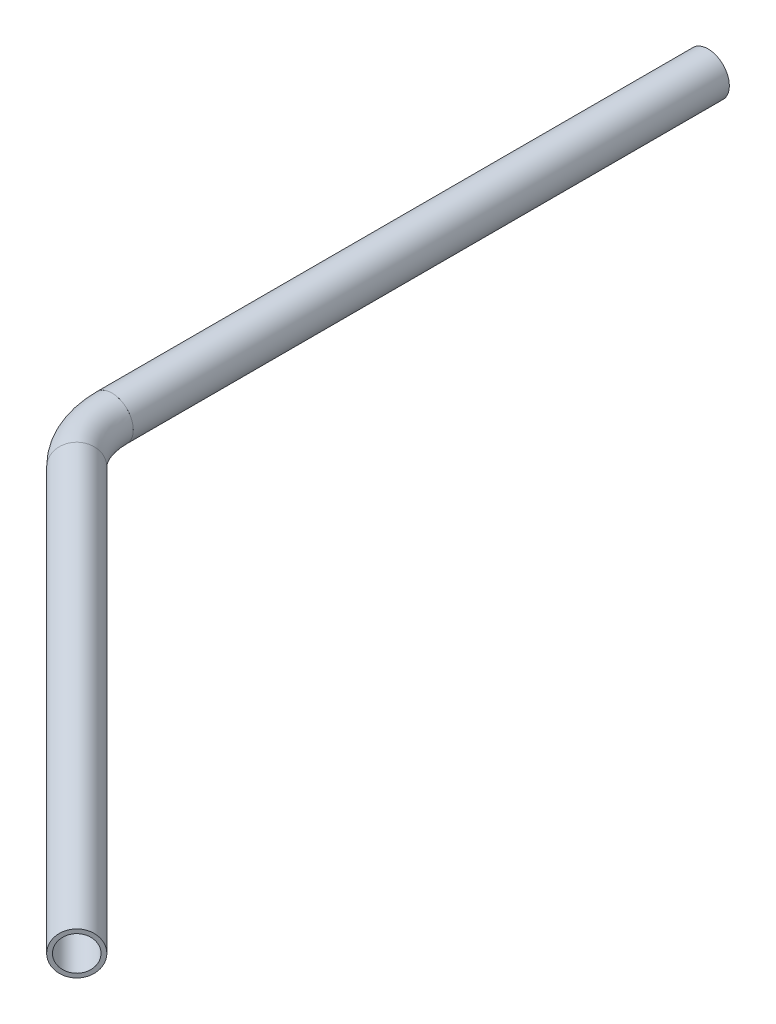
SolidWorks part; units mm, degrees
ref_plane "Ebene vorne" through (0, 0, 0) normal (0, 0, 1) x (1, 0, 0)
ref_plane "Ebene oben" through (0, 0, 0) normal (0, 1, 0) x (1, 0, 0)
ref_plane "Ebene rechts" through (0, 0, 0) normal (1, 0, 0) x (0, 0, -1)
sketch "Layout-Skizze" plane through (0, 0, 0) normal (0, 1, 0) x (1, 0, 0)
  line L0 (0, 27.918) -> (0, 500)
  line L1 (19.741, -19.741) -> (353.5534, -353.5534)
  arc A0 (0, 27.918) -> (19.741, -19.741) centre (67.4, 27.918) ccw
  point P7 (0, 0)
  dimension "D4" = 67.4
  dimension "D1" = 500
  dimension "D2" = 500
  dimension "W" = 45
other "Strukturbauteil2"
ref_plane "Ebene3" through (0, 0, -27.918) normal (0, 0, -1) x (-1, 0, 0)
sketch "Skizze1" plane through (0, 0, -27.918) normal (0, 0, -1) x (-1, 0, 0)
  circle A0 centre (0, 0) radius 16.85
  circle A1 centre (0, 0) radius 13.6
  point P3 (0, 0)
  dimension "D" = 33.7
  dimension "s" = 3.25
